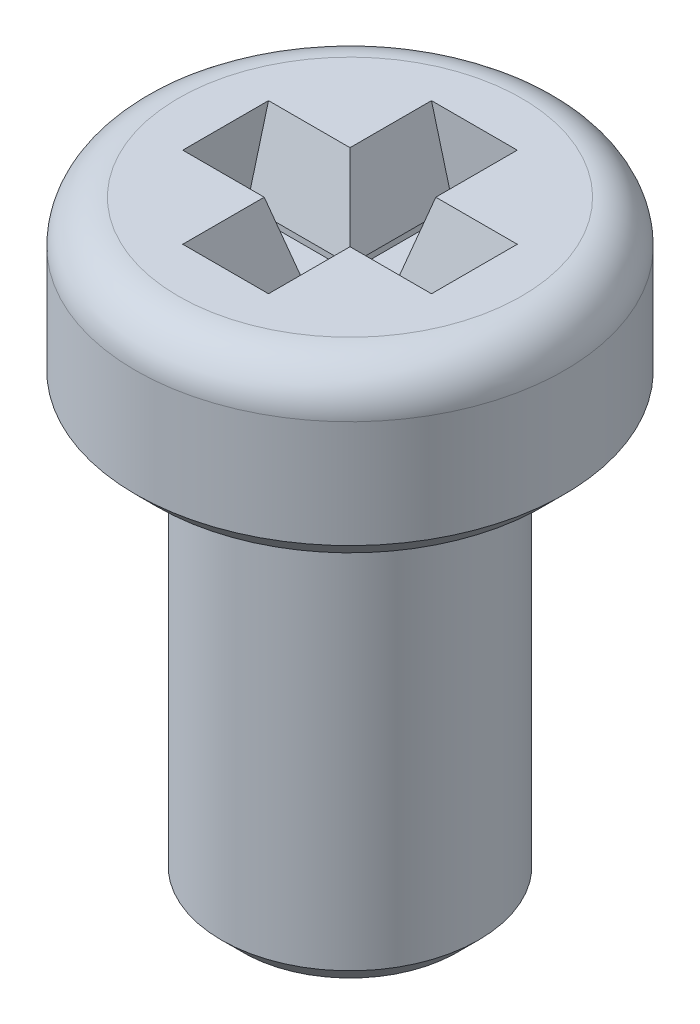
SolidWorks part; units mm, degrees
ref_plane "Alzado" through (0, 0, 0) normal (0, 0, 1) x (1, 0, 0)
ref_plane "Planta" through (0, 0, 0) normal (0, 1, 0) x (1, 0, 0)
ref_plane "Vista lateral" through (0, 0, 0) normal (1, 0, 0) x (0, 0, -1)
sketch "Croquis1" plane through (0, 0, 0) normal (0, 1, 0) x (1, 0, 0)
  circle A0 centre (0, 0) radius 2.5
  dimension "D1" = 5
extrude "Saliente-Extruir1" add sketch "Croquis1" along normal blind 2
sketch "Croquis2" plane through (0, 0, 0) normal (0, -1, 0) x (1, 0, 0)
  circle A0 centre (0, 0) radius 1.5
  dimension "D1" = 3
extrude "Saliente-Extruir2" add sketch "Croquis2" along normal blind 5
chamfer "Chaflán1" distance 0.25 angle 45 2 edges at (0, -5, -1.5) (0, 0, 2.5)
fillet "Redondeo1" radius 0.5 1 edges at (0, 2, 2.5)
sketch "Croquis3" plane through (0, 2, 0) normal (0, 1, 0) x (1, 0, 0)
  line L0 (0.25, 0.25) -> (1.45, 0.25)
  line L1 (-0.25, 1.45) -> (0.25, 1.45)
  line L2 (-0.25, 1.45) -> (-0.25, 0.25)
  line L3 (-0.25, -1.45) -> (0.25, -1.45)
  line L4 (0.25, 1.45) -> (0.25, 0.25)
  line L5 (-1.45, -0.25) -> (-0.25, -0.25)
  line L6 (-1.45, -0.25) -> (-1.45, 0.25)
  line L7 (-1.45, 0.25) -> (-0.25, 0.25)
  line L8 (1.45, -0.25) -> (1.45, 0.25)
  line L9 (-0.25, -0.25) -> (-0.25, -1.45)
  line L10 (0.25, -0.25) -> (0.25, -1.45)
  line L11 (0.25, -0.25) -> (1.45, -0.25)
  line L12 (-0.25, 0.25) -> (0.25, -0.25) construction
  line L13 (0.25, 0.25) -> (-0.25, -0.25) construction
  line L14 (-0.25, 0.25) -> (-0.25, -0.25) construction
  line L15 (0.25, -0.25) -> (-0.25, -0.25) construction
  point P12 (0, 0)
  dimension "D1" = 0.5
  dimension "D2" = 0.5
  dimension "D3" = 1.2
  dimension "D4" = 1.2
  dimension "D5" = 1.2
  dimension "D6" = 1.2
extrude "Cortar-Extruir1" cut sketch "Croquis3" against normal blind 1
chamfer "Chaflán2" distance 0.25 angle 75 8 edges at (-0.25, 2, 0.85) (-0.85, 2, 0.25) (0.25, 2, 0.85) (0.85, 2, 0.25) (0.85, 2, -0.25) (0.25, 2, -0.85) (-0.85, 2, -0.25) (-0.25, 2, -0.85)
